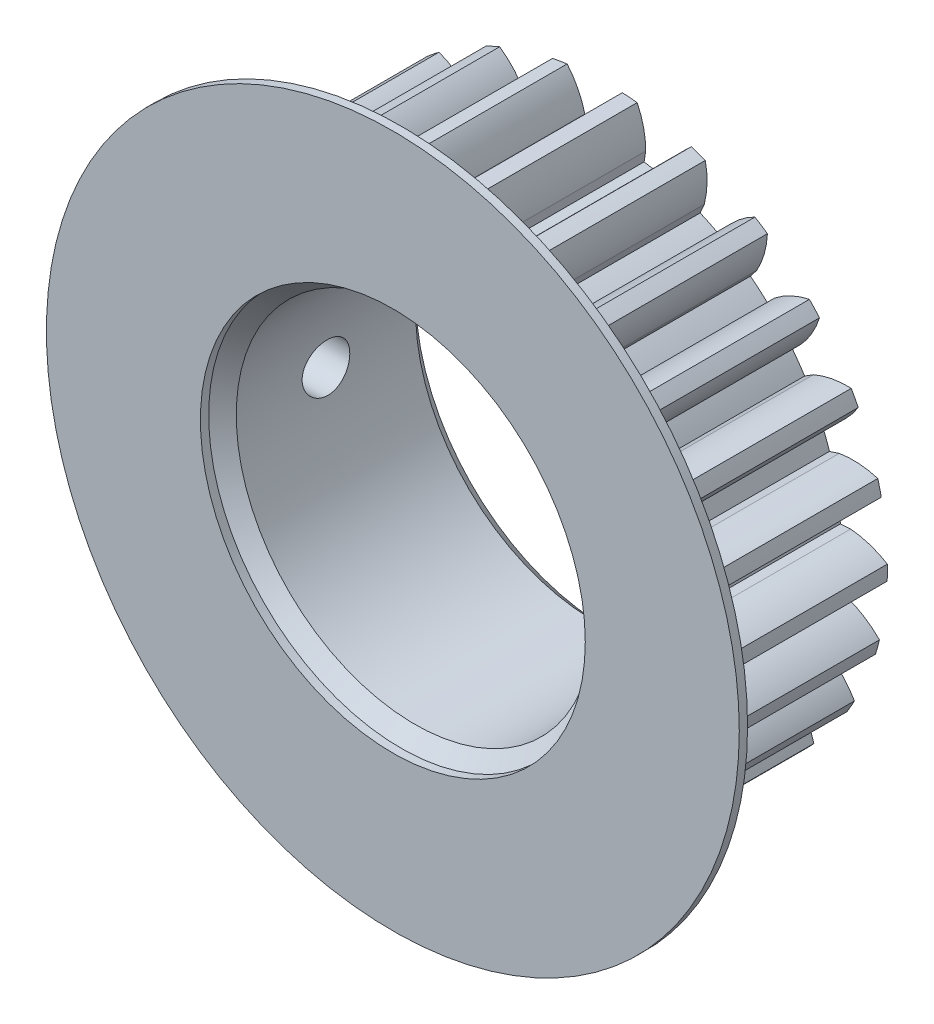
SolidWorks part; units mm, degrees
ref_plane "Front Plane" through (0, 0, 0) normal (0, 0, 1) x (1, 0, 0)
ref_plane "Top Plane" through (0, 0, 0) normal (0, 1, 0) x (1, 0, 0)
ref_plane "Right Plane" through (0, 0, 0) normal (1, 0, 0) x (0, 0, -1)
sketch "Sketch2" plane through (0, 0, 0) normal (0, 0, 1) x (1, 0, 0)
  circle A0 centre (0, 0) radius 20.25
  dimension "D1" = 40.5
extrude "gear outside diameter" add sketch "Sketch2" along normal blind 15
sketch "Sketch1" plane through (0, 0, 0) normal (0, 0, 1) x (1, 0, 0)
  line L0 (0, 17.6192) -> (0, 0) construction
  line L1 (0, 0) -> (0.2794, 18.7479) construction
  line L2 (0, 0) -> (1.0338, 20.2236) construction
  line L3 (0, 0) -> (-0.7489, 15.6134) construction
  line L4 (0, 17.6192) -> (0, 16.875)
  line L5 (-1.6863, 17.5384) -> (-1.6151, 16.7975)
  circle A0 centre (0, 0) radius 20.25 construction
  circle A1 centre (0, 0) radius 18.75 construction
  circle A2 centre (0, 0) radius 17.6192 construction
  arc A3 (1.0338, 20.2236) -> (0, 17.6192) centre (6.0814, 16.7125) ccw
  arc A4 (-2.9647, 20.0318) -> (-1.6863, 17.5384) centre (-7.653, 16.0537) cw
  arc A5 (-2.9647, 20.0318) -> (1.0338, 20.2236) centre (0, 0) cw
  arc A6 (0, 16.875) -> (-1.6151, 16.7975) centre (0, 0) ccw
  dimension "D1" = 40.5
  dimension "D2" = 37.5
  dimension "D3" = 35.2385
  dimension "D7" = 33.75
  dimension "D4" = 3.6
  dimension "D5" = 0.854
  dimension "D6" = 2.926
extrude "gear tooth cut" cut sketch "Sketch1" along normal through all
pattern_circular "gear teeth" count 25 over 360 about axis through (0, 0, 0) along (0, 0, 1) of "gear tooth cut"
sketch "Sketch3" plane through (0, 0, 0) normal (0, 0, 1) x (1, 0, 0)
  circle A0 centre (0, 0) radius 16.875
  dimension "D1" = 33.75
extrude "gear dedendum circle" add sketch "Sketch3" along normal up to surface (15 mm away) up to face at (0, 0, 15)
sketch "Sketch4" plane through (0, 0, 15) normal (0, 0, 1) x (1, 0, 0)
  circle A0 centre (0, 0) radius 12.95
  dimension "D1" = 25.9
extrude "Cut-Extrude1" cut sketch "Sketch4" against normal through all
chamfer "Chamfer1" distance 1 angle 45 2 edges at (12.95, 0, 0) (12.95, 0, 15)
hole_wizard "#8-32 Tapped Hole1" positions "3DSketch1" profile "Sketch5" tap size "#8-32" standard "ANSI Inch"
sketch3d "3DSketch1"
  line L1 (-20.2472, -0.3358, 15) -> (-20.2472, -0.3358, 0)
  arc A2 (-19.1215, -6.6657, 15) -> (-18.739, -7.6753, 15) centre (0, 0, 15) ccw construction
  arc A3 (-19.1215, -6.6657, 0) -> (-18.739, -7.6753, 0) centre (0, 0, 0) ccw construction
  point P23 (0, 0, 35.25)
  point P27 (0, 0, 20.25)
  point P44 (-20.2472, -0.3358, 7.5)
sketch "Sketch5" plane through (-20.2472, -0.3358, 7.5) normal (0, 0, 1) x (0.0166, -0.9999, 0)
  line L0 (0, 0) -> (0, 7.3)
  line L1 (0, 7.3) -> (1.7272, 7.3)
  line L2 (1.7272, 7.3) -> (1.7272, 0)
  line L5 (1.7272, 0) -> (0, 0)
  line L11 (0, -6.35) -> (0, 107.95) construction
  dimension "Thru Tap Drill Dia." = 3.4544
  dimension "Thru Tap Drill Depth" = 7.3
sketch "Sketch6" plane through (0, 0, 15) normal (0, 0, 1) x (1, 0, 0)
  circle A0 centre (0, 0) radius 25.1128
  circle A1 centre (0, 0) radius 13.95 construction
  circle A2 centre (0, 0) radius 13.95
  point P0 (-2.0152, 25.0318)
  dimension "D1" = 5
extrude "Boss-Extrude1" add sketch "Sketch6" along normal blind 0.6
equation "\"N\" = 25'Number of teeth"
equation "\"m\"= 1.5'module  (using 25.4/P for imperial gears)"
equation "\"F\"= 15'face width"
equation "\"phi\"=20 'pressure angle"
equation "\"d\"=\"N\"*\"m\""
equation "\"OD\"=(\"N\"+2)*\"m\""
equation "\"db\"=\"d\"* cos( \"phi\" ) "
equation "\"D5@Sketch1\"= (tan( \"phi\" )-\"phi\" * pi /180)*180/ pi "
equation "\"D2@Sketch1\" = \"d\""
equation "\"D3@Sketch1\"=\"db\""
equation "\"D1@Sketch1\"=\"OD\""
equation "\"phiB\"= arccos( \"db\"/\"OD\" ) "
equation "\"D6@Sketch1\"=tan(\"phiB\")*180 /  pi -\"phiB\""
equation "\"D4@Sketch1\" = 360/\"N\"/4"
equation "\"D1@Sketch2\" = \"OD\""
equation "\"D1@gear teeth\"=\"N\""
equation "\"x\"=2.5-\"N\"*(1-cos(\"phi\"))"
equation "\"D1@Sketch3\" = (\"N\"-2.5)*\"m\""
equation "\"D7@Sketch1\" = (\"N\"-2.5)*\"m\""
equation "\"D1@gear outside diameter\" = \"F\""
